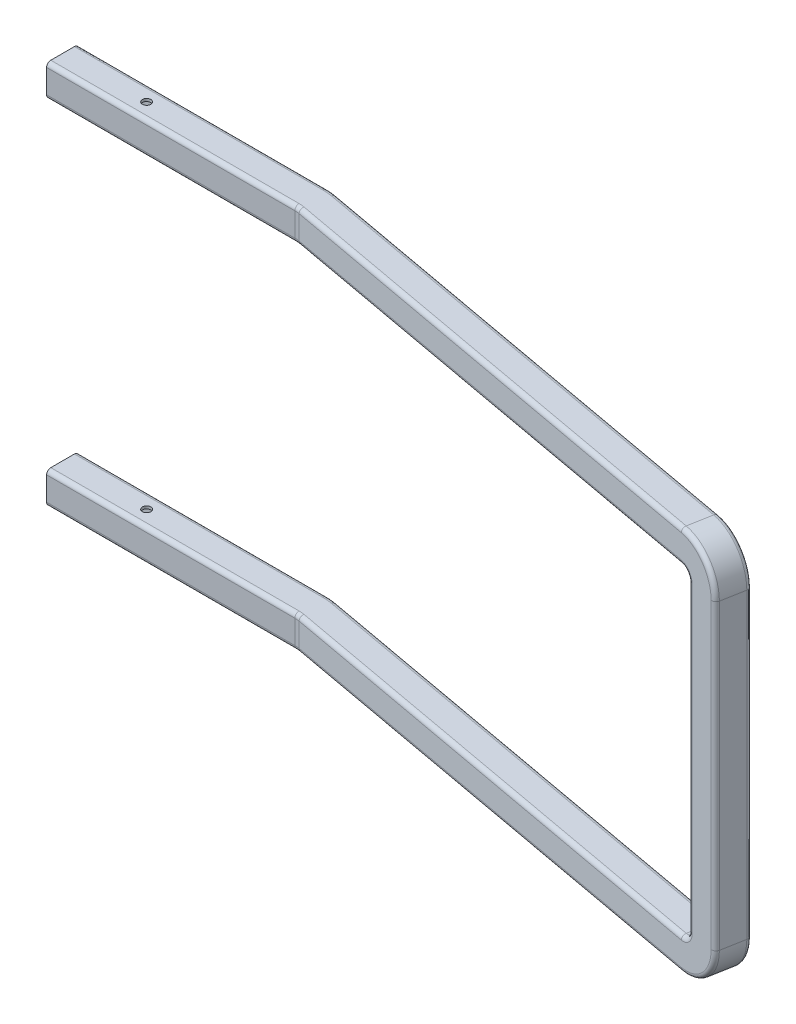
SolidWorks part; units mm, degrees
other "Markup1" [suppressed]
sketch "Sketch29" [suppressed] plane through (-50, 12.7, -12.7) normal (-0.6703, 0.7401, -0.0544) x (0.7356, 0.653, -0.1804)
sketch "Sketch30" [suppressed] plane through (-50, 20, -18.6944) normal (-0.6703, 0.7401, -0.0544) x (0.7356, 0.653, -0.1804)
sketch "Sketch34" [suppressed] plane through (-50, 20, -18.6944) normal (-0.6703, 0.7401, -0.0544) x (0.7356, 0.653, -0.1804)
sketch "Sketch35" [suppressed] plane through (-50, 30, -28.5496) normal (-0.6703, 0.7401, -0.0544) x (0.7356, 0.653, -0.1804)
sketch "Sketch36" [suppressed] plane through (-50, 30, -28.5496) normal (-0.6703, 0.7401, -0.0544) x (0.7356, 0.653, -0.1804)
sketch "Sketch37" plane through (-50, 30, -28.5496) normal (-0.6703, 0.7401, -0.0544) x (0.7356, 0.653, -0.1804)
sketch "Sketch38" plane through (-50, 25, -25) normal (-0.6703, 0.7401, -0.0544) x (0.7356, 0.653, -0.1804)
sketch "Sketch39" plane through (-50, 19.05, -19.05) normal (-0.6703, 0.7401, -0.0544) x (0.7356, 0.653, -0.1804)
material "5052-O"
ref_plane "Front Plane" through (0, 0, 0) normal (0, 0, 1) x (1, 0, 0)
ref_plane "Top Plane" through (0, 0, 0) normal (0, 1, 0) x (1, 0, 0)
ref_plane "Right Plane" through (0, 0, 0) normal (1, 0, 0) x (0, 0, -1)
sketch "Sketch2" plane through (0, 0, 0) normal (1, 0, 0) x (0, 0, -1)
  line L1 (-14.05, -19.05) -> (14.05, -19.05)
  line L2 (-19.05, -14.05) -> (-19.05, 14.05)
  line L3 (-14.05, 19.05) -> (14.05, 19.05)
  line L4 (19.05, -14.05) -> (19.05, 14.05)
  line L5 (-19.05, -19.05) -> (19.05, 19.05) construction
  line L6 (-19.05, 19.05) -> (19.05, -19.05) construction
  arc A0 (19.05, -14.05) -> (14.05, -19.05) centre (14.05, -14.05) cw
  arc A1 (-14.05, -19.05) -> (-19.05, -14.05) centre (-14.05, -14.05) cw
  arc A2 (-19.05, 14.05) -> (-14.05, 19.05) centre (-14.05, 14.05) cw
  arc A3 (14.05, 19.05) -> (19.05, 14.05) centre (14.05, 14.05) cw
  point P0 (0, 0)
  dimension "D3" = 5
  dimension "D1" = 38.1
  dimension "D2" = 38.1
sketch3d "3DSketch2"
  line L0 (0, 0, 0) -> (840.2912, 0, 0) construction
  line L1 (840.2912, 0, 0) -> (840.2912, -210, 0) construction
  line L2 (840.2912, -210, 0) -> (840.2912, -210, 107.5) construction
  line L3 (0, 0, 0) -> (245.4843, 0, 0)
  line L4 (254.4426, 0, 0.8091) -> (810.7767, 0, 102.125)
  line L5 (0, 0, 0) -> (-50, 0, 0)
  line L6 (0, 0, 0) -> (0, -210, 0) construction
  line L7 (840.2912, -210, 107.5) -> (840.2912, -210, 287.5) construction
  line L8 (840.2912, -210, 287.5) -> (-9.7834, -210, 287.5) construction
  line L9 (840.2912, -30, 107.5) -> (840.2912, -210, 107.5)
  arc A0 (254.4426, 0, 0.8091) -> (245.4843, 0, 0) centre (245.4843, 0, 50) ccw
  arc A1 (840.2912, -30, 107.5) -> (810.7767, 0, 102.125) centre (810.7767, -30, 102.125) ccw
  point P16 (250, 0, 0)
  point P17 (245.4843, 50, 50)
  point P20 (840.2912, 0, 107.5)
  point P21 (805.4017, -30, 131.6396)
  dimension "5" = 50
  dimension "D9" = 30
  dimension "D1" = 250
  dimension "D2" = 50
  dimension "D3" = 210
  dimension "D4" = 107.5
  dimension "D5" = 210
  dimension "D6" = 600
  dimension "D7" = 180
  dimension "D8" = 210
sweep "Sweep-Thin3" add profiles "Sketch2" path "3DSketch2" parameters "D1"=3.175
sketch "Sketch21" plane through (0, 0, 0) normal (0, 1, 0) x (1, 0, 0)
  line L0 (0, 0) -> (245.4843, 0) construction
  circle A0 centre (50, 0) radius 5
  dimension "D1" = 10
  dimension "D2" = 50
extrude "Cut-Extrude3" cut sketch "Sketch21" against normal through all both and the other way through all
sketch "Sketch22" [suppressed] plane through (0, 0, 0) normal (0, 0, 1) x (1, 0, 0)
ref_plane "Plane1" [suppressed] through (0, -210, 0) normal (0, 1, 0) x (1, 0, 0)
ref_plane "Plane2" through (0, -210, 0) normal (0, -1, 0) x (-1, 0, 0)
ref_plane "Plane3" through (0, -210, 0) normal (0, -1, 0) x (-1, 0, 0)
mirror "Mirror1" about plane through (0, -210, 0) normal (0, -1, 0) of "Cut-Extrude3", "Sweep-Thin3"
ref_plane "Plane4" [suppressed] through (2.91, 0, -15.9792) normal (-0.1792, 0, 0.9838) x (0.9838, 0, 0.1792)
sketch "Sketch23" [suppressed] plane through (2.91, 0, -15.9792) normal (-0.1792, 0, 0.9838) x (0.9838, 0, 0.1792)
  line L0 (874.5043, -30) -> (874.5043, -390) construction
  line L1 (874.5043, 30) -> (674.5043, 30)
  line L2 (874.5043, 30) -> (874.5043, -450)
  line L3 (874.5043, -450) -> (674.5043, -450)
  line L4 (674.5043, 30) -> (674.5043, -450)
  line L5 (868.2597, -30) -> (868.2597, -390) construction
  point P8 (868.2597, -210)
  point P9 (874.5043, -210)
  dimension "D1" = 480
  dimension "D2" = 200
extrude "Boss-Extrude1" [suppressed] add sketch "Sketch23" along normal blind 25.4
sketch "Sketch25" [suppressed] plane through (2.91, 0, -15.9792) normal (0.1792, 0, -0.9838) x (-0.9838, 0, -0.1792)
  line L0 (-674.5043, -22.305) -> (-674.5043, -397.695) construction
  line L1 (-816.5543, -174.3) -> (-732.4543, -174.3) construction
  line L2 (-816.5543, -174.3) -> (-816.5543, -245.7) construction
  line L3 (-816.5543, -245.7) -> (-732.4543, -245.7) construction
  line L4 (-732.4543, -174.3) -> (-732.4543, -245.7) construction
  line L5 (-816.5543, -174.3) -> (-732.4543, -245.7) construction
  line L6 (-816.5543, -245.7) -> (-732.4543, -174.3) construction
  line L7 (-874.5043, 30) -> (-674.5043, 30) construction
  line L8 (-729.1662, -177.588) -> (-735.7423, -171.012) construction
  line L9 (-732.525, -180.9468) -> (-739.1011, -174.3707)
  line L10 (-725.8075, -174.2293) -> (-732.3836, -167.6532)
  line L11 (-732.4543, -210) -> (-816.5543, -210) construction
  line L12 (-774.5043, -174.3) -> (-774.5043, -245.7) construction
  line L13 (-729.1662, -242.412) -> (-735.7423, -248.988) construction
  line L14 (-732.525, -239.0532) -> (-739.1011, -245.6293)
  line L15 (-725.8075, -245.7707) -> (-732.3836, -252.3468)
  line L16 (-819.8423, -242.412) -> (-813.2662, -248.988) construction
  line L17 (-816.4836, -239.0532) -> (-809.9075, -245.6293)
  line L18 (-823.2011, -245.7707) -> (-816.625, -252.3468)
  line L19 (-819.8423, -177.588) -> (-813.2662, -171.012) construction
  line L20 (-816.4836, -180.9468) -> (-809.9075, -174.3707)
  line L21 (-823.2011, -174.2293) -> (-816.625, -167.6532)
  arc A0 (-732.525, -180.9468) -> (-725.8075, -174.2293) centre (-729.1662, -177.588) ccw
  arc A1 (-732.3836, -167.6532) -> (-739.1011, -174.3707) centre (-735.7423, -171.012) ccw
  arc A2 (-732.525, -239.0532) -> (-725.8075, -245.7707) centre (-729.1662, -242.412) cw
  arc A3 (-732.3836, -252.3468) -> (-739.1011, -245.6293) centre (-735.7423, -248.988) cw
  arc A4 (-816.4836, -239.0532) -> (-823.2011, -245.7707) centre (-819.8423, -242.412) ccw
  arc A5 (-816.625, -252.3468) -> (-809.9075, -245.6293) centre (-813.2662, -248.988) ccw
  arc A6 (-816.4836, -180.9468) -> (-823.2011, -174.2293) centre (-819.8423, -177.588) cw
  arc A7 (-816.625, -167.6532) -> (-809.9075, -174.3707) centre (-813.2662, -171.012) cw
  point P0 (-774.5043, -210)
  point P7 (-674.5043, -210)
  point P10 (-774.5043, 30)
  point P13 (-732.4543, -174.3)
  point P24 (-732.4543, -245.7)
  point P31 (-816.5543, -245.7)
  point P38 (-816.5543, -174.3)
  dimension "D1" = 71.4
  dimension "D2" = 84.1
  dimension "D3" = 45
  dimension "D4" = 9.5
  dimension "D5" = 9.3
extrude "Cut-Extrude4" [suppressed] cut sketch "Sketch25" against normal through all
ref_plane "Plane7" [suppressed] through (661.9492, 30, 129.8584) normal (0, -1, 0) x (-1, 0, 0)
sketch "Sketch28" [suppressed] plane through (-1.6408, 0, 9.0097) normal (-0.1792, 0, 0.9838) x (0.9838, 0, 0.1792)
  line L0 (874.5043, 30) -> (674.5043, 30) construction
  line L1 (717.3543, -159.2) -> (831.6543, -159.2)
  line L2 (717.3543, -159.2) -> (717.3543, -260.8)
  line L3 (717.3543, -260.8) -> (831.6543, -260.8)
  line L4 (831.6543, -159.2) -> (831.6543, -260.8)
  line L5 (717.3543, -159.2) -> (831.6543, -260.8) construction
  line L6 (717.3543, -260.8) -> (831.6543, -159.2) construction
  line L7 (674.5043, 30) -> (674.5043, -450) construction
  point P0 (774.5043, -210)
  point P7 (774.5043, 30)
  point P10 (674.5043, -210)
  dimension "D1" = 101.6
  dimension "D2" = 114.3
fillet "Fillet1" [suppressed] radius 30
fillet "Fillet2" [suppressed] radius 0.9144
ref_plane "Plane5" [suppressed] through (0, 0, 0) normal (-1, 0, 0) x (0, 0, 1)
ref_plane "EndOfTubePlane" [suppressed] through (140, 0, 0) normal (-1, 0, 0) x (0, 0, 1)
split line "Split Line1" [suppressed]
split line "Split Line2" [suppressed]
ref_plane "Plane8" [suppressed] through (806.7804, -391.4504, 124.0691) normal (0.9838, 0, 0.1792) x (0.1792, 0, -0.9838)
sketch "Sketch33" [suppressed] plane through (0, 0, 0) normal (0, 1, 0) x (1, 0, 0)
  line L0 (140, -28.5496) -> (245.4843, -28.5496) construction
  line L1 (249.3275, -28.8967) -> (665.6004, -104.7056) construction
  line L2 (-50, -28.5496) -> (140, -28.5496) construction
  arc A0 (140, -28.5496) -> (365.0664, -49.9743) centre (273.909, 185.2905) ccw
rib "Rib4" [suppressed] sketch "Sketch33" sketch "Sketch33" thickness 10 extrusion direction parallel to sketch draft on no parameters "D1"=10
chamfer "Chamfer1" [suppressed] distance 2.5 angle 45
mirror "Mirror2" [suppressed] about plane through (0, -210, 0) normal (0, -1, 0)
